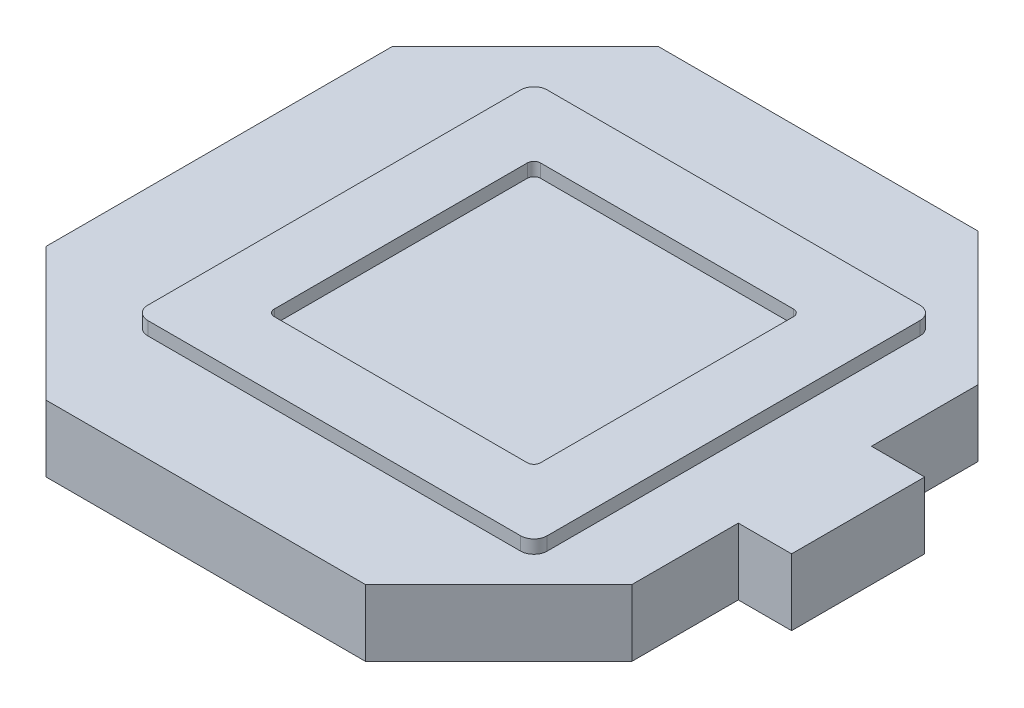
SolidWorks part; units mm, degrees
ref_plane "Plan de face" through (0, 0, 0) normal (0, 0, 1) x (1, 0, 0)
ref_plane "Plan de dessus" through (0, 0, 0) normal (0, 1, 0) x (1, 0, 0)
ref_plane "Plan de droite" through (0, 0, 0) normal (1, 0, 0) x (0, 0, -1)
sketch "Esquisse1" plane through (0, 0, 0) normal (0, 1, 0) x (1, 0, 0)
  line L0 (22, 13) -> (12.003, 23)
  line L1 (22, 13) -> (22, 5)
  line L2 (-22, -13) -> (-22, 13)
  line L3 (22, 5) -> (26, 5)
  line L4 (22, -5) -> (22, -13)
  line L5 (-22, -13) -> (22, 13) construction
  line L6 (-22, 13) -> (22, -13) construction
  line L7 (12.003, 23) -> (-12.003, 23)
  line L8 (-12.003, 23) -> (-22, 13)
  line L9 (-22, -13) -> (-12.003, -23)
  line L10 (-12.003, -23) -> (12.003, -23)
  line L11 (12.003, -23) -> (22, -13)
  line L12 (0, 23) -> (0, 0) construction
  line L13 (0, 0) -> (0, -23) construction
  line L14 (22, -5) -> (26, -5)
  line L15 (26, 5) -> (26, -5)
  point P1 (0, 0)
  dimension "D1" = 26
  dimension "D2" = 44
  dimension "D3" = 23
  dimension "D4" = 23
  dimension "D5" = 14.14
  dimension "D6" = 14.14
  dimension "D7" = 14.14
  dimension "D8" = 14.14
  dimension "D9" = 8
  dimension "D10" = 8
  dimension "D11" = 4
extrude "Boss.-Extru.1" add sketch "Esquisse1" along normal blind 5
sketch "Esquisse2" plane through (0, 5, 0) normal (0, 1, 0) x (1, 0, 0)
  line L0 (-13.3545, 15) -> (-13.3545, -15)
  line L1 (11.6455, -10) -> (-8.3545, -10)
  line L2 (11.6455, 10) -> (11.6455, -10)
  line L3 (-8.3545, -10) -> (-8.3545, 10)
  line L4 (-8.3545, 10) -> (11.6455, 10)
  line L5 (16.6455, 15) -> (16.6455, -15)
  line L6 (16.6455, -15) -> (-13.3545, -15)
  line L7 (16.6455, 15) -> (-13.3545, 15)
  line L8 (-22, 13) -> (-22, -13) construction
  line L10 (12.003, 23) -> (-12.003, 23) construction
  line L12 (-12.003, -23) -> (12.003, -23) construction
  dimension "D1" = 30
  dimension "D2" = 30
  dimension "D3" = 5
  dimension "D4" = 5
  dimension "D5" = 5
  dimension "D6" = 5
  dimension "D7" = 8
  dimension "D8" = 8
extrude "Boss.-Extru.2" add sketch "Esquisse2" along normal blind 1
sketch "Esquisse3" plane through (0, 0, 0) normal (0, -1, 0) x (1, 0, 0)
  line L0 (-12.003, 23) -> (12.003, 23) construction
  line L1 (-16, 17) -> (-11, 17)
  line L2 (-16, 17) -> (-16, 11.8)
  line L3 (-16, 11.8) -> (-11, 11.8)
  line L4 (-11, 17) -> (-11, 11.8)
  line L5 (-16, 17) -> (-11, 11.8) construction
  line L6 (-16, 11.8) -> (-11, 17) construction
  line L8 (-22, -13) -> (-22, 13) construction
  line L9 (12.003, -23) -> (-12.003, -23) construction
  line L10 (-16, -17) -> (-10.8, -17)
  line L11 (-16, -17) -> (-16, -11.8)
  line L12 (-16, -11.8) -> (-10.8, -11.8)
  line L13 (-10.8, -17) -> (-10.8, -11.8)
  line L14 (-16, -17) -> (-10.8, -11.8) construction
  line L15 (-16, -11.8) -> (-10.8, -17) construction
  line L16 (11.8, -11.8) -> (17, -11.8)
  line L17 (11.8, -11.8) -> (11.8, -17)
  line L18 (11.8, -17) -> (17, -17)
  line L19 (17, -11.8) -> (17, -17)
  line L20 (11.8, -11.8) -> (17, -17) construction
  line L21 (11.8, -17) -> (17, -11.8) construction
  line L22 (10.8, 11.8) -> (16, 11.8)
  line L23 (10.8, 11.8) -> (10.8, 17)
  line L24 (10.8, 17) -> (16, 17)
  line L25 (16, 11.8) -> (16, 17)
  line L26 (10.8, 11.8) -> (16, 17) construction
  line L27 (10.8, 17) -> (16, 11.8) construction
  line L28 (22, -5) -> (22, -13) construction
  line L29 (22, 13) -> (22, 5) construction
  line L31 (-2.5, -2.5) -> (2.5, -2.5)
  line L32 (-2.5, -2.5) -> (-2.5, 2.5)
  line L33 (-2.5, 2.5) -> (2.5, 2.5)
  line L34 (2.5, -2.5) -> (2.5, 2.5)
  line L35 (-2.5, -2.5) -> (2.5, 2.5) construction
  line L36 (-2.5, 2.5) -> (2.5, -2.5) construction
  point P0 (-13.5, 14.4)
  point P9 (-13.4, -14.4)
  point P14 (14.4, -14.4)
  point P19 (13.4, 14.4)
  point P30 (0, 0)
  dimension "D1" = 5
  dimension "D2" = 5.2
  dimension "D3" = 6
  dimension "D4" = 6
  dimension "D5" = 5.2
  dimension "D6" = 5.2
  dimension "D7" = 5.2
  dimension "D8" = 5.2
  dimension "D9" = 5.2
  dimension "D10" = 5.2
  dimension "D11" = 6
  dimension "D12" = 6
  dimension "D13" = 6
  dimension "D14" = 5
  dimension "D15" = 6
  dimension "D16" = 6
  dimension "D17" = 5
  dimension "D18" = 5
  dimension "D19" = 20.5
  dimension "D20" = 20.5
  dimension "D21" = 19.5
  dimension "D22" = 19.5
extrude "Enlèv. mat.-Extru.1" cut sketch "Esquisse3" against normal blind 4.8
fillet "Congé1" radius 1 4 edges at (16.6455, 5.5, -15) (-13.3545, 5.5, -15) (-13.3545, 5.5, 15) (16.6455, 5.5, 15)
fillet "Congé2" radius 0.5 4 edges at (-8.3545, 5.5, 10) (-8.3545, 5.5, -10) (11.6455, 5.5, -10) (11.6455, 5.5, 10)
